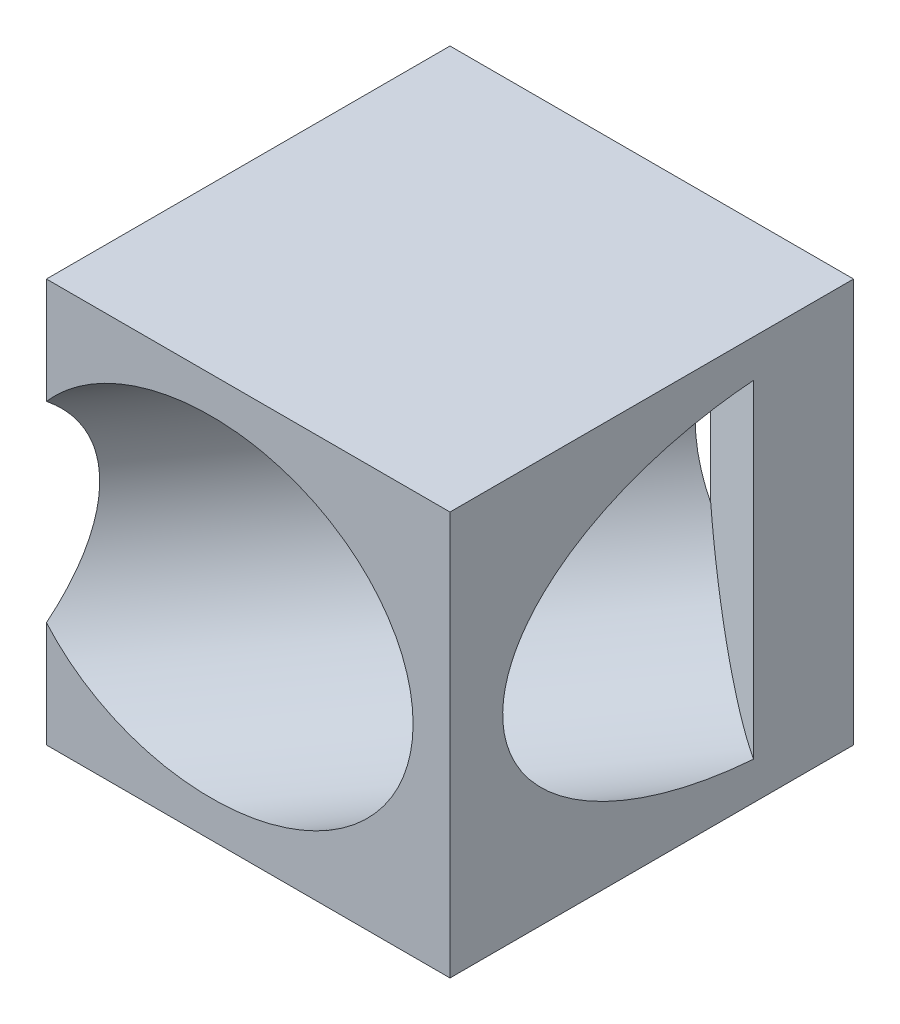
SolidWorks part; units mm, degrees
material "ABS"
ref_plane "Front Plane" through (0, 0, 0) normal (0, 0, 1) x (1, 0, 0)
ref_plane "Top Plane" through (0, 0, 0) normal (0, 1, 0) x (1, 0, 0)
ref_plane "Right Plane" through (0, 0, 0) normal (1, 0, 0) x (0, 0, -1)
sketch "Sketch1" plane through (0, 0, 0) normal (0, 0, 1) x (1, 0, 0)
  line L1 (-70, 50) -> (70, 50)
  line L2 (-70, 50) -> (-70, -50)
  line L3 (-70, -50) -> (70, -50)
  line L4 (70, 50) -> (70, -50)
  line L5 (-70, 50) -> (70, -50) construction
  line L6 (-70, -50) -> (70, 50) construction
  point P0 (0, 0)
  dimension "D1" = 100
  dimension "D2" = 140
extrude "Boss-Extrude1" add sketch "Sketch1" along normal blind 100
ref_plane "Plane1" through (-70.0139, 0, 99.9902) normal (-0.5736, 0, 0.8192) x (0, -1, 0)
sketch "Sketch2" plane through (-70.0139, 0, 99.9902) normal (-0.5736, 0, 0.8192) x (0, -1, 0)
  line L0 (0, 117.9206) -> (0, -34.2201) construction
  line L1 (-50, 0.017) -> (50, 0.017) construction
  circle A0 centre (0, 58.017) radius 41
  point P4 (0, 0.017)
  dimension "D1" = 82
  dimension "D2" = 58
extrude "Cut-Extrude1" cut sketch "Sketch2" against normal through all
sketch "Sketch3" plane through (0, 0, 100) normal (0, 0, 1) x (1, 0, 0)
  line L0 (-70, -50) -> (70, -50) construction
  line L1 (-70, 50) -> (-50, 50)
  line L2 (-70, 50) -> (-70, -50)
  line L3 (-70, -50) -> (-50, -50)
  line L4 (-50, 50) -> (-50, -50)
  dimension "D1" = 20
extrude "Cut-Extrude2" cut sketch "Sketch3" against normal through all
sketch "Sketch4" plane through (0, 0, 100) normal (0, 0, 1) x (1, 0, 0)
  line L0 (-50, -50) -> (70, -50) construction
  line L1 (-50, 50) -> (-40, 50)
  line L2 (-50, 50) -> (-50, -50)
  line L3 (-50, -50) -> (-40, -50)
  line L4 (-40, 50) -> (-40, -50)
  line L6 (70, 50) -> (60, 50)
  line L7 (70, 50) -> (70, -50)
  line L8 (70, -50) -> (60, -50)
  line L9 (60, 50) -> (60, -50)
  dimension "D1" = 10
  dimension "D2" = 10
extrude "Cut-Extrude3" cut sketch "Sketch4" against normal through all
ref_plane "Plane2" through (19.7394, 0, -28.1908) normal (0.5736, 0, -0.8192) x (-0.8192, 0, -0.5736)
sketch "Sketch5" plane through (19.7394, 0, -28.1908) normal (0.5736, 0, -0.8192) x (-0.8192, 0, -0.5736)
  circle A0 centre (-58.017, 0) radius 41
extrude "Boss-Extrude2" add sketch "Sketch5" against normal blind 20.3
sketch "Sketch6" plane through (0, 50, 0) normal (0, 1, 0) x (1, 0, 0)
  line L0 (60, 0) -> (-40, 0)
  line L1 (64.2446, -2.9721) -> (-24.7658, 59.3537) construction
  line L2 (60, 0) -> (60, -100) construction
  line L3 (-40, 0) -> (-40, 38.6222)
  line L4 (-40, 38.6222) -> (122.4682, 38.6222)
  line L5 (122.4682, 38.6222) -> (119.9263, -91.2591)
  line L6 (119.9263, -91.2591) -> (60, -91.2591)
  line L7 (60, -91.2591) -> (60, 0)
extrude "Cut-Extrude4" cut sketch "Sketch6" against normal through all
